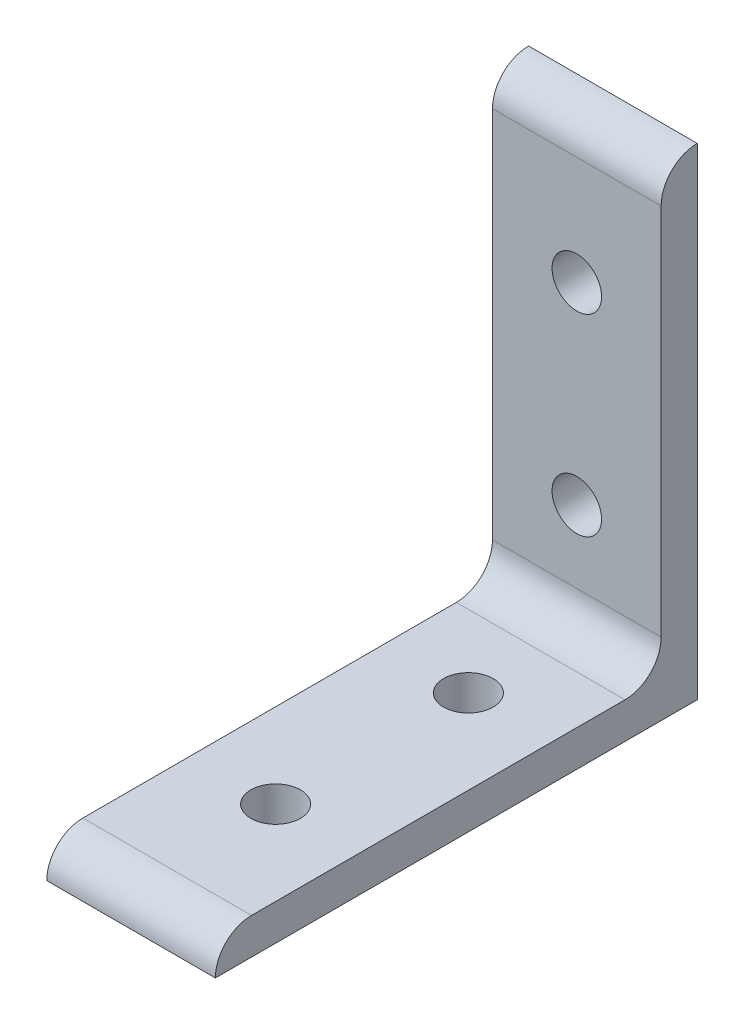
SolidWorks part; units mm, degrees
ref_plane "Front Plane" through (0, 0, 0) normal (0, 0, 1) x (1, 0, 0)
ref_plane "Top Plane" through (0, 0, 0) normal (0, 1, 0) x (1, 0, 0)
ref_plane "Right Plane" through (0, 0, 0) normal (1, 0, 0) x (0, 0, -1)
ref_plane "Plane1" through (11.1125, 0, 0) normal (1, 0, 0) x (0, 0, -1)
sketch "Sketch1" plane through (11.1125, 0, 0) normal (1, 0, 0) x (0, 0, -1)
  line L0 (-4.7678, 58.7428) -> (-4.7678, 4.7678)
  line L1 (-4.7678, 4.7678) -> (-58.7428, 4.7678)
  line L2 (-63.5053, 0.0053) -> (-0.0053, 0.0053)
  line L3 (-0.0053, 0.0053) -> (-0.0053, 63.5053)
  arc A0 (-58.7428, 4.7678) -> (-63.5053, 0.0053) centre (-58.7428, 0.0053) ccw
  arc A1 (-0.0053, 63.5053) -> (-4.7678, 58.7428) centre (-0.0053, 58.7428) ccw
extrude "Boss-Extrude1" add sketch "Sketch1" against normal blind 22.225
hole_wizard "M6 Clearance Hole1" positions "Sketch3" profile "Sketch2" hole size "M6" standard "Ansi Metric"
sketch "Sketch3" plane through (0, 0.0053, 0) normal (0, -1, 0) x (1, 0, 0)
  point P0 (0, 19.0553)
  point P1 (0, 44.4553)
sketch "Sketch2" plane through (0, 0.0053, 19.0553) normal (1, 0, 0) x (0, 0, -1)
  line L0 (0, 0) -> (0, 63.5)
  line L1 (0, 63.5) -> (3.2639, 63.5)
  line L2 (3.2639, 63.5) -> (3.2639, 0)
  line L5 (3.2639, 0) -> (0, 0)
  line L11 (0, -6.35) -> (0, 107.95) construction
  dimension "Thru Hole Dia." = 6.5278
  dimension "Thru Hole Depth" = 63.5
hole_wizard "M6 Clearance Hole2" positions "Sketch5" profile "Sketch4" hole size "M6" standard "Ansi Metric"
sketch "Sketch5" plane through (0, 0, 0.0053) normal (0, 0, -1) x (-1, 0, 0)
  point P0 (0, 19.0553)
  point P1 (0, 44.4553)
sketch "Sketch4" plane through (0, 19.0553, 0.0053) normal (1, 0, 0) x (0, 1, 0)
  line L0 (0, 0) -> (0, 63.5)
  line L1 (0, 63.5) -> (3.2639, 63.5)
  line L2 (3.2639, 63.5) -> (3.2639, 0)
  line L5 (3.2639, 0) -> (0, 0)
  line L11 (0, -6.35) -> (0, 107.95) construction
  dimension "Thru Hole Dia." = 6.5278
  dimension "Thru Hole Depth" = 63.5
fillet "Fillet1" radius 4.7625 1 edges at (0, 4.7678, 4.7678)
